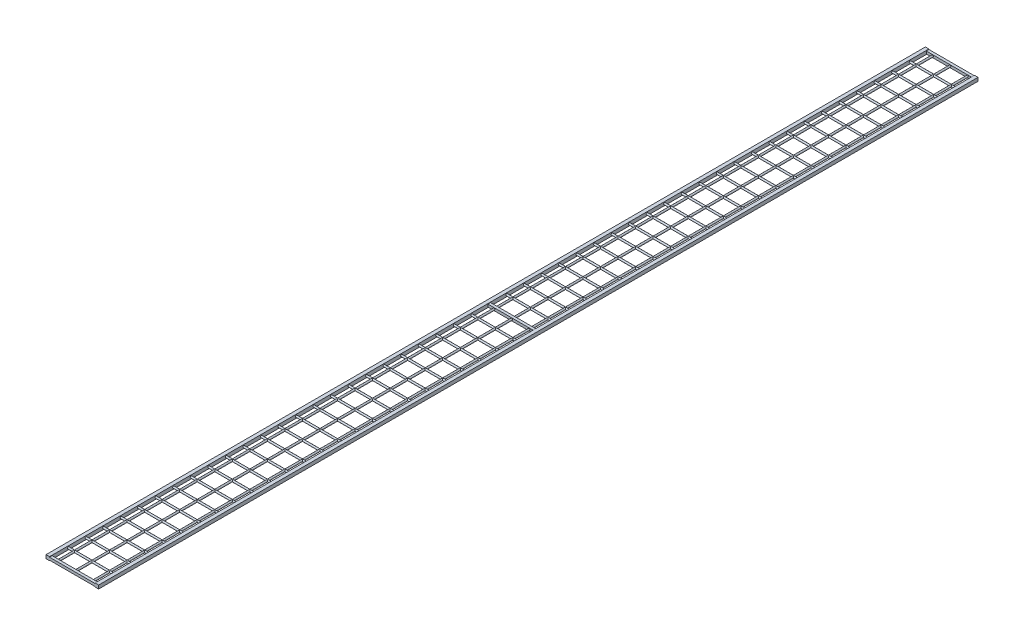
SolidWorks part; units mm, degrees
ref_plane "Piano frontale" through (0, 0, 0) normal (0, 0, 1) x (1, 0, 0)
ref_plane "Piano superiore" through (0, 0, 0) normal (0, 1, 0) x (1, 0, 0)
ref_plane "Piano destro" through (0, 0, 0) normal (1, 0, 0) x (0, 0, -1)
sketch "Schizzo2" plane through (0, 0, 0) normal (0, 0, 1) x (1, 0, 0)
  line L0 (0, 0) -> (5.716, 0) construction
  line L1 (0, 0) -> (50, 0) construction
  circle A0 centre (0, 0) radius 2.5
  circle A1 centre (50, 0) radius 2.5
  circle A2 centre (100, 0) radius 2.5
  circle A3 centre (150, 0) radius 2.5
  circle A4 centre (200, 0) radius 2.5
  circle A5 centre (250, 0) radius 2.5
  circle A6 centre (300, 0) radius 2.5
  circle A7 centre (350, 0) radius 2.5
  circle A8 centre (400, 0) radius 2.5
  circle A9 centre (450, 0) radius 2.5
  circle A10 centre (500, 0) radius 2.5
  circle A11 centre (550, 0) radius 2.5
  circle A12 centre (600, 0) radius 2.5
  circle A13 centre (650, 0) radius 2.5
  circle A14 centre (700, 0) radius 2.5
  circle A15 centre (750, 0) radius 2.5
  circle A16 centre (800, 0) radius 2.5
  circle A17 centre (850, 0) radius 2.5
  circle A18 centre (900, 0) radius 2.5
  dimension "D1" = 50
  dimension "D2" = 19
extrude "Estrusione-Estrusione1" add sketch "Schizzo2" along normal blind 2500 contours A0
sketch "Schizzo3" plane through (0, 0, 0) normal (1, 0, 0) x (0, 0, -1)
  line L0 (0, 0) -> (-50, 0) construction
  circle A0 centre (0, 0) radius 2.5
  circle A1 centre (-50, 0) radius 2.5
  circle A2 centre (-100, 0) radius 2.5
  circle A3 centre (-150, 0) radius 2.5
  circle A4 centre (-200, 0) radius 2.5
  circle A5 centre (-250, 0) radius 2.5
  circle A6 centre (-300, 0) radius 2.5
  circle A7 centre (-350, 0) radius 2.5
  circle A8 centre (-400, 0) radius 2.5
  circle A9 centre (-450, 0) radius 2.5
  circle A10 centre (-500, 0) radius 2.5
  circle A11 centre (-550, 0) radius 2.5
  circle A12 centre (-600, 0) radius 2.5
  circle A13 centre (-650, 0) radius 2.5
  circle A14 centre (-700, 0) radius 2.5
  circle A15 centre (-750, 0) radius 2.5
  circle A16 centre (-800, 0) radius 2.5
  circle A17 centre (-850, 0) radius 2.5
  circle A18 centre (-900, 0) radius 2.5
  circle A19 centre (-950, 0) radius 2.5
  circle A20 centre (-1000, 0) radius 2.5
  circle A21 centre (-1050, 0) radius 2.5
  circle A22 centre (-1100, 0) radius 2.5
  circle A23 centre (-1150, 0) radius 2.5
  circle A24 centre (-1200, 0) radius 2.5
  circle A25 centre (-1250, 0) radius 2.5
  circle A26 centre (-1300, 0) radius 2.5
  circle A27 centre (-1350, 0) radius 2.5
  circle A28 centre (-1400, 0) radius 2.5
  circle A29 centre (-1450, 0) radius 2.5
  circle A30 centre (-1500, 0) radius 2.5
  circle A31 centre (-1550, 0) radius 2.5
  circle A32 centre (-1600, 0) radius 2.5
  circle A33 centre (-1650, 0) radius 2.5
  circle A34 centre (-1700, 0) radius 2.5
  circle A35 centre (-1750, 0) radius 2.5
  circle A36 centre (-1800, 0) radius 2.5
  circle A37 centre (-1850, 0) radius 2.5
  circle A38 centre (-1900, 0) radius 2.5
  circle A39 centre (-1950, 0) radius 2.5
  circle A40 centre (-2000, 0) radius 2.5
  circle A41 centre (-2050, 0) radius 2.5
  circle A42 centre (-2100, 0) radius 2.5
  circle A43 centre (-2150, 0) radius 2.5
  circle A44 centre (-2200, 0) radius 2.5
  circle A45 centre (-2250, 0) radius 2.5
  circle A46 centre (-2300, 0) radius 2.5
  circle A47 centre (-2350, 0) radius 2.5
  circle A48 centre (-2400, 0) radius 2.5
  circle A49 centre (-2450, 0) radius 2.5
  circle A50 centre (-2500, 0) radius 2.5
  dimension "D1" = 51
  dimension "D2" = 50
extrude "Estrusione-Estrusione2" add sketch "Schizzo3" against normal blind 27.5 and the other way blind 922.5
sketch "Schizzo5" plane through (-27.5, 0, 0) normal (-1, 0, 0) x (0, 0, 1)
  line L0 (1246.25, 3.75) -> (1253.75, 3.75)
  line L1 (-3.75, 3.75) -> (3.75, 3.75)
  line L2 (-3.75, 3.75) -> (-3.75, -3.75)
  line L3 (-3.75, -3.75) -> (3.75, -3.75)
  line L4 (3.75, 3.75) -> (3.75, -3.75)
  line L5 (1246.25, 3.75) -> (1246.25, -3.75)
  line L6 (1246.25, -3.75) -> (1253.75, -3.75)
  line L7 (1253.75, 3.75) -> (1253.75, -3.75)
  line L8 (2496.25, 3.75) -> (2503.75, 3.75)
  line L9 (2496.25, 3.75) -> (2496.25, -3.75)
  line L10 (2496.25, -3.75) -> (2503.75, -3.75)
  line L11 (2503.75, 3.75) -> (2503.75, -3.75)
  line L12 (-3.75, 3.75) -> (1246.25, 3.75) construction
  dimension "D1" = 7.5
  dimension "D2" = 7.5
  dimension "D3" = 3.75
  dimension "D4" = 3.75
  dimension "D5" = 1250
extrude "Estrusione-Estrusione3" add sketch "Schizzo5" against normal up to surface (950 mm away)
sketch "Schizzo7" plane through (0, 0, -3.75) normal (0, 0, -1) x (-1, 0, 0)
  line L0 (27.5, 3.75) -> (27.5, -3.75) construction
  line L1 (27.5, -5) -> (17.5, -5)
  line L2 (27.5, -5) -> (27.5, 5)
  line L3 (27.5, 5) -> (17.5, 5)
  line L4 (17.5, -5) -> (17.5, 5)
  line L5 (-922.5, -3.75) -> (27.5, -3.75) construction
  line L6 (-912.5, -5) -> (-912.5, 5)
  line L7 (-912.5, -5) -> (-922.5, -5)
  line L8 (-922.5, -5) -> (-922.5, 5)
  line L9 (-912.5, 5) -> (-922.5, 5)
  dimension "D1" = 10
  dimension "D2" = 10
  dimension "D3" = 10
  dimension "D4" = 1.25
  dimension "D5" = 950
extrude "Estrusione-Estrusione4" add sketch "Schizzo7" against normal up to surface (2507.5 mm away)
sketch "Schizzo8" plane through (0, 0, 2503.75) normal (0, 0, 1) x (1, 0, 0)
  line L0 (-27.5, -5) -> (-27.5, 5) construction
  line L1 (122.5, 24.5677) -> (1050.5342, 24.5677)
  line L2 (122.5, 24.5677) -> (122.5, -49.7845)
  line L3 (122.5, -49.7845) -> (1050.5342, -49.7845)
  line L4 (1050.5342, 24.5677) -> (1050.5342, -49.7845)
  dimension "D1" = 150
extrude "Taglio-Estrusione1" cut sketch "Schizzo8" against normal up to surface (2507.5 mm away)
sketch "Schizzo9" plane through (0, 0, 2503.75) normal (0, 0, 1) x (1, 0, 0)
  line L1 (112.5, 5) -> (122.5, 5)
  line L2 (112.5, 5) -> (112.5, -5)
  line L3 (112.5, -5) -> (122.5, -5)
  line L4 (122.5, 5) -> (122.5, -5)
  line L7 (122.5, 3.75) -> (-17.5, 3.75) construction
  line L8 (122.5, 3.75) -> (122.5, -3.75) construction
  dimension "D1" = 10
  dimension "D2" = 10
  dimension "D3" = 1.25
  dimension "D4" = 0
extrude "Estrusione-Estrusione5" add sketch "Schizzo9" against normal up to surface (2507.5 mm away)
